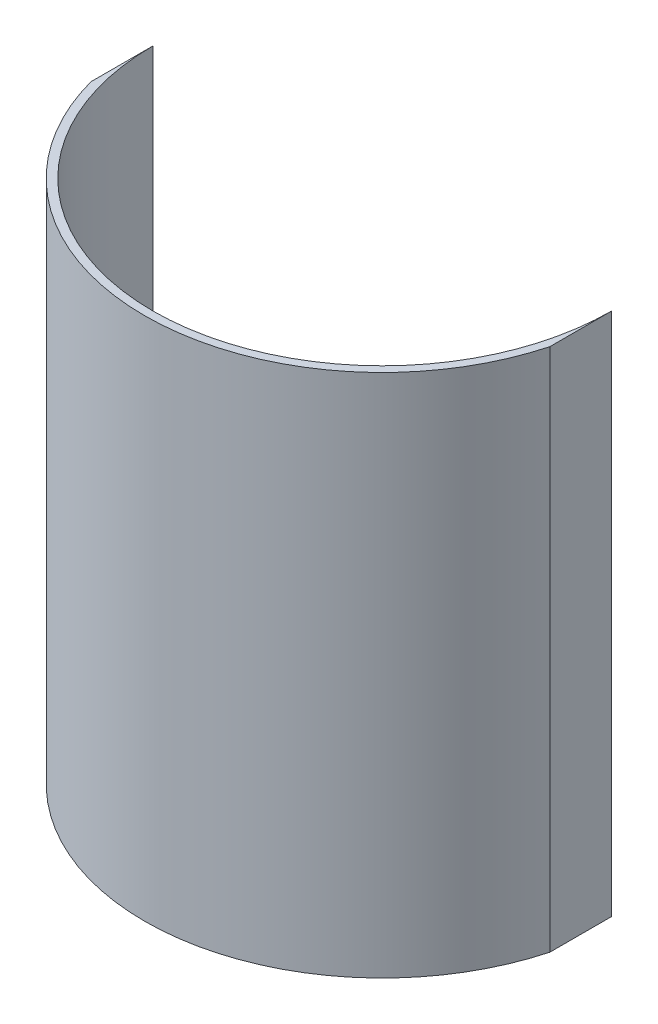
SolidWorks part; units mm, degrees
ref_plane "Front Plane" through (0, 0, 0) normal (0, 0, 1) x (1, 0, 0)
ref_plane "Top Plane" through (0, 0, 0) normal (0, 1, 0) x (1, 0, 0)
ref_plane "Right Plane" through (0, 0, 0) normal (1, 0, 0) x (0, 0, -1)
sketch "Sketch1" plane through (0, 0, 0) normal (0, 1, 0) x (1, 0, 0)
  circle A0 centre (0, 0) radius 88.9
  circle A1 centre (0, 0) radius 92.075
  dimension "D1" = 177.8
  dimension "D2" = 184.15
sketch "Sketch2" plane through (0, 0, 0) normal (0, 0, 1) x (1, 0, 0)
  line L0 (0, 0) -> (0, 304.8) construction
  line L1 (88.9, 304.8) -> (-88.9, 304.8) construction
  line L2 (-92.075, 152.4) -> (92.075, 152.4) construction
  line L3 (-92.075, 304.8) -> (-92.075, 0) construction
  line L4 (92.075, 0) -> (92.075, 304.8) construction
  line L6 (-88.9, 50.8) -> (88.9, 50.8)
  line L7 (-88.9, 50.8) -> (-88.9, 254)
  line L8 (-88.9, 254) -> (88.9, 254)
  line L9 (88.9, 50.8) -> (88.9, 254)
  line L10 (-88.9, 50.8) -> (88.9, 254) construction
  line L11 (-88.9, 254) -> (88.9, 50.8) construction
  point P11 (0, 152.4)
  dimension "D1" = 177.8
  dimension "D2" = 203.2
sketch "Sketch3" plane through (0, 50.8, 0) normal (0, 1, 0) x (1, 0, 0)
  line L2 (88.9, -23.9707) -> (88.9, 0)
  line L3 (-88.9, 0) -> (-88.9, -23.9707)
  line L4 (88.9, -23.9707) -> (88.9, 0)
  line L5 (-88.9, 0) -> (-88.9, -23.9707)
  arc A2 (-88.9, -23.9707) -> (88.9, -23.9707) centre (0, 0) ccw
  arc A3 (-88.9, 0) -> (88.9, 0) centre (0, 0) ccw
  arc A4 (-88.9, -23.9707) -> (88.9, -23.9707) centre (0, 0) ccw
  arc A5 (-88.9, 0) -> (88.9, 0) centre (0, 0) ccw
  dimension "D1" = 0
extrude "Boss-Extrude2" add sketch "Sketch3" along normal blind 203.2 separate body
